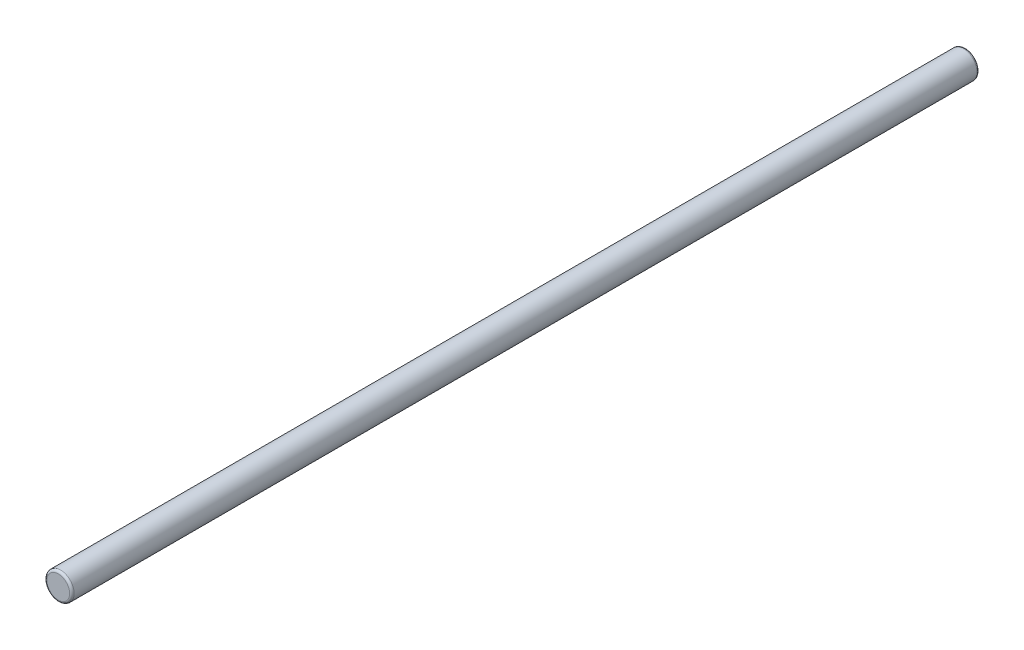
SolidWorks part; units mm, degrees
ref_plane "Front Plane" through (0, 0, 0) normal (0, 0, 1) x (1, 0, 0)
ref_plane "Top Plane" through (0, 0, 0) normal (0, 1, 0) x (1, 0, 0)
ref_plane "Right Plane" through (0, 0, 0) normal (1, 0, 0) x (0, 0, -1)
sketch "Sketch1" plane through (0, 0, 0) normal (0, 0, 1) x (1, 0, 0)
  circle A0 centre (0, 0) radius 1.5
extrude "Boss-Extrude1" add sketch "Sketch1" along normal blind 100
fillet "Fillet1" radius 0.25 2 edges at (1.5, 0, 0) (1.5, 0, 100)
